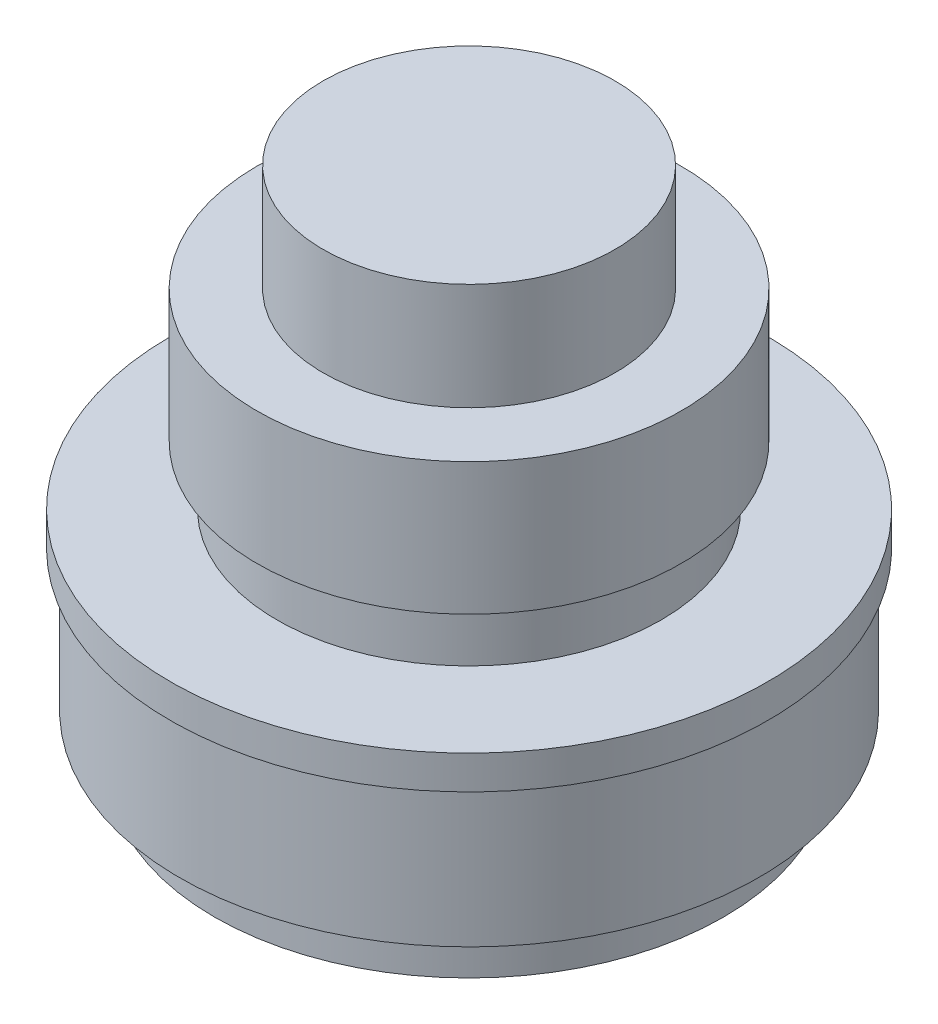
SolidWorks part; units mm, degrees
ref_plane "Front Plane" through (0, 0, 0) normal (0, 0, 1) x (1, 0, 0)
ref_plane "Top Plane" through (0, 0, 0) normal (0, 1, 0) x (1, 0, 0)
ref_plane "Right Plane" through (0, 0, 0) normal (1, 0, 0) x (0, 0, -1)
sketch "Sketch3" plane through (0, 0, 0) normal (0, 0, 1) x (1, 0, 0)
  line L0 (0, 5.6622) -> (0, -39.9378)
  line L1 (0, 5.6622) -> (-12.71, 5.6622)
  line L2 (-12.71, 5.6622) -> (-12.71, -3.6378)
  line L3 (-12.71, -3.6378) -> (-18.46, -3.6378)
  line L4 (-18.46, -3.6378) -> (-18.46, -15.1378)
  line L5 (-18.46, -15.1378) -> (-16.715, -15.1378)
  line L6 (-16.715, -15.1378) -> (-16.715, -20.2678)
  line L7 (-16.715, -20.2678) -> (-26.005, -20.2678)
  line L8 (-26.005, -20.2678) -> (-26.005, -23.1935)
  line L9 (-26.005, -23.1935) -> (-25.2, -23.1935)
  line L10 (-25.2, -23.1935) -> (-25.2, -35.4435)
  line L11 (-25.2, -35.4435) -> (-22.155, -35.4435)
  line L12 (-22.155, -35.4435) -> (-22.155, -39.9378)
  line L13 (-22.155, -39.9378) -> (0, -39.9378)
  dimension "D1" = 45.6
  dimension "D2" = 12.71
  dimension "D3" = 9.3
  dimension "D4" = 5.75
  dimension "D5" = 11.5
  dimension "D6" = 1.745
  dimension "D7" = 5.13
  dimension "D8" = 9.29
  dimension "D9" = 12.25
  dimension "D10" = 3.045
  dimension "D11" = 0.805
revolve "Revolve1" add sketch "Sketch3" angle 360 about L0
